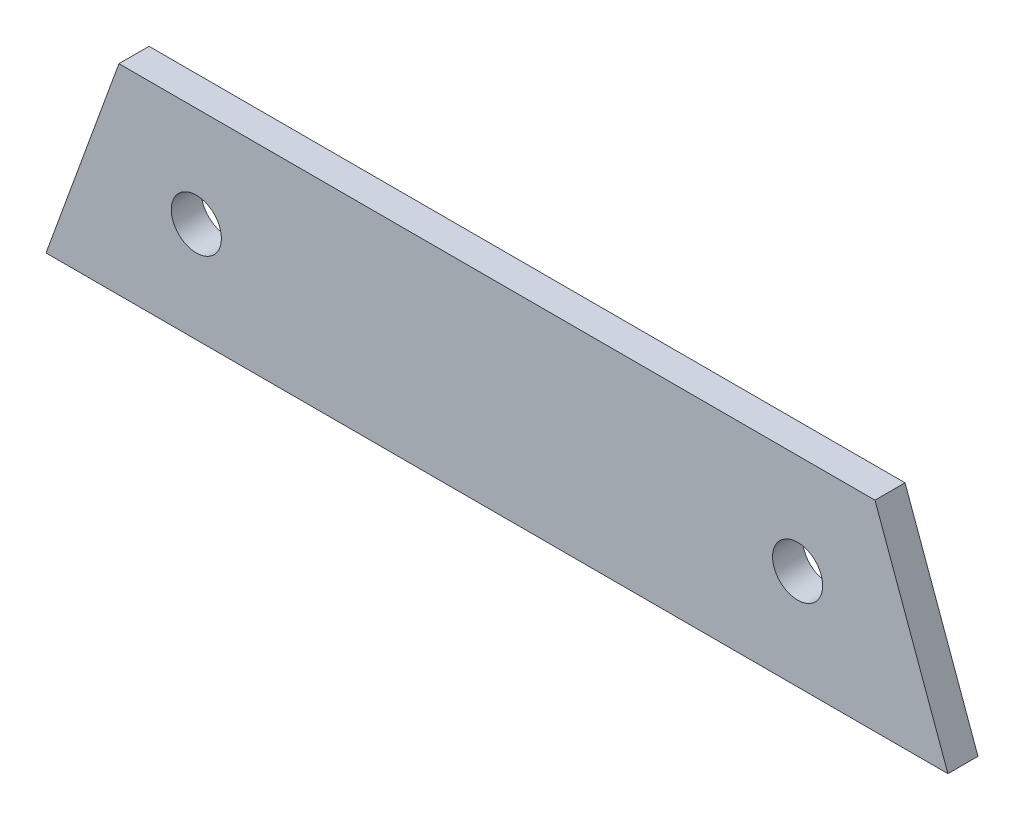
SolidWorks part; units mm, degrees
ref_plane "Alzado" through (0, 0, 0) normal (0, 0, 1) x (1, 0, 0)
ref_plane "Planta" through (0, 0, 0) normal (0, 1, 0) x (1, 0, 0)
ref_plane "Vista lateral" through (0, 0, 0) normal (1, 0, 0) x (0, 0, -1)
sketch "Croquis1" plane through (0, 0, 0) normal (0, 0, 1) x (1, 0, 0)
  line L0 (-45, 0) -> (45, 0)
  line L1 (45, 0) -> (37.7206, 20)
  line L2 (37.7206, 20) -> (-37.7206, 20)
  line L3 (-37.7206, 20) -> (-45, 0)
  circle A0 centre (-30, 10) radius 2.5
  circle A1 centre (30, 10) radius 2.5
  dimension "D9" = 5
  dimension "D1" = 90
  dimension "D2" = 45
  dimension "D3" = 20
  dimension "D4" = 70
  dimension "D5" = 70
  dimension "D6" = 10
  dimension "D7" = 15
  dimension "D8" = 75
extrude "Saliente-Extruir1" add sketch "Croquis1" along normal blind 3
